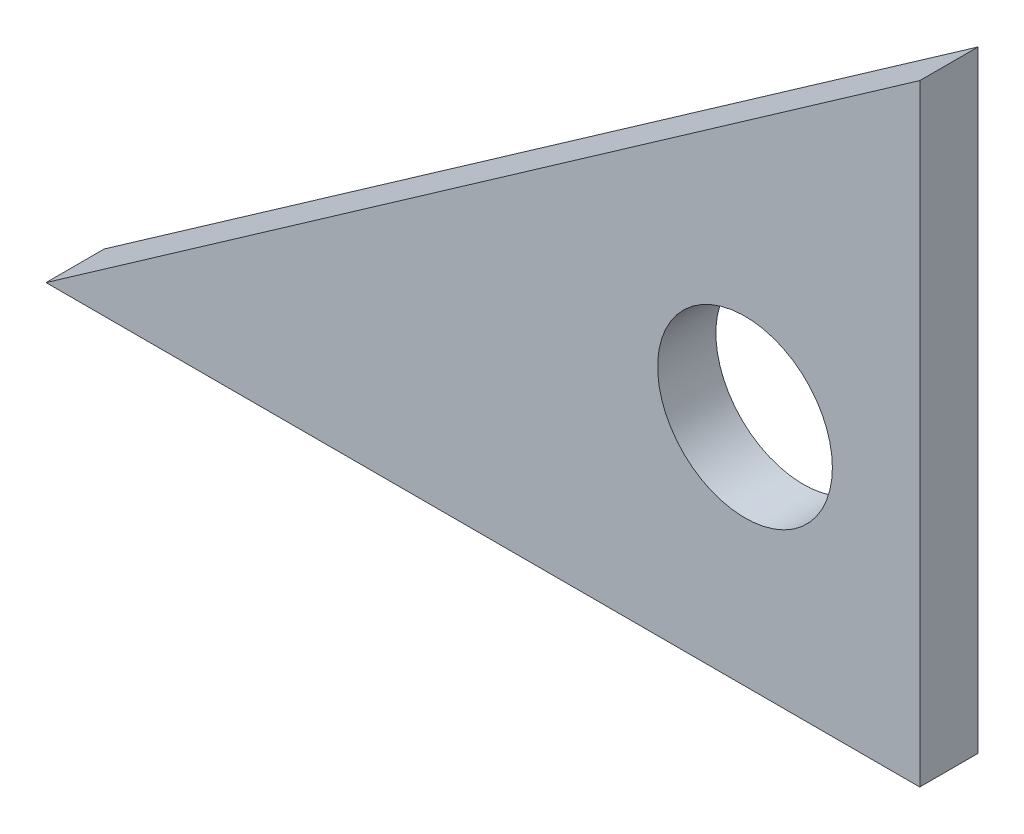
SolidWorks part; units mm, degrees
ref_plane "Front Plane" through (0, 0, 0) normal (0, 0, 1) x (1, 0, 0)
ref_plane "Top Plane" through (0, 0, 0) normal (0, 1, 0) x (1, 0, 0)
ref_plane "Right Plane" through (0, 0, 0) normal (1, 0, 0) x (0, 0, -1)
sketch "Sketch1" plane through (0, 0, 0) normal (0, 0, 1) x (1, 0, 0)
  line L0 (0, 0) -> (95.25, 66.6948)
  line L1 (95.25, 66.6948) -> (95.25, 0)
  line L2 (95.25, 0) -> (0, 0)
  dimension "D1" = 95.25
  dimension "D2" = 35
  dimension "D3" = 90
extrude "Boss-Extrude1" add sketch "Sketch1" along normal blind 6.35 contours L0 L1 L2
sketch "Sketch2" plane through (0, 0, 6.35) normal (0, 0, 1) x (1, 0, 0)
  line L0 (95.25, 66.6948) -> (95.25, 0) construction
  line L1 (95.25, 0) -> (0, 0) construction
  circle A0 centre (76.2, 25.4) radius 9.525
  dimension "D1" = 19.05
  dimension "D2" = 19.05
  dimension "D3" = 25.4
extrude "Cut-Extrude1" cut sketch "Sketch2" against normal blind 6.35
